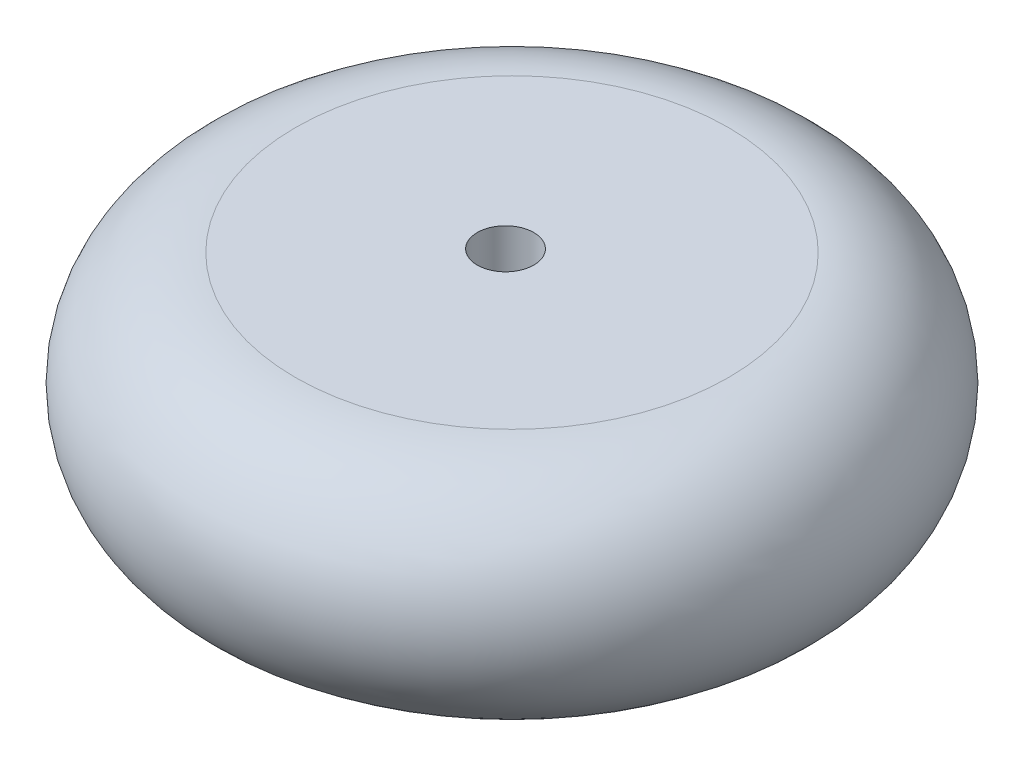
SolidWorks part; units mm, degrees
ref_plane "前视基准面" through (0, 0, 0) normal (0, 0, 1) x (1, 0, 0)
ref_plane "上视基准面" through (0, 0, 0) normal (0, 1, 0) x (1, 0, 0)
ref_plane "右视基准面" through (0, 0, 0) normal (1, 0, 0) x (0, 0, -1)
sketch "草图1" plane through (0, 0, 0) normal (0, 0, 1) x (1, 0, 0)
  line L0 (-10, 0) -> (10, 0) construction
  line L1 (-10, 12) -> (13, 12)
  line L2 (-10, -12) -> (13, -12)
  line L3 (13, 12) -> (13, -12)
  arc A0 (-10, 12) -> (-10, -12) centre (-10, 0) ccw
  point P3 (0, 0)
  dimension "D2" = 12
  dimension "D1" = 23
  dimension "D3" = 24
revolve "旋转1" add sketch "草图1" angle 360 about L3
sketch "草图2" plane through (0, -12, 0) normal (0, -1, 0) x (1, 0, 0)
  circle A0 centre (12.3109, 0) radius 3
  dimension "D1" = 6
extrude "切除-拉伸1" cut sketch "草图2" against normal up to next
